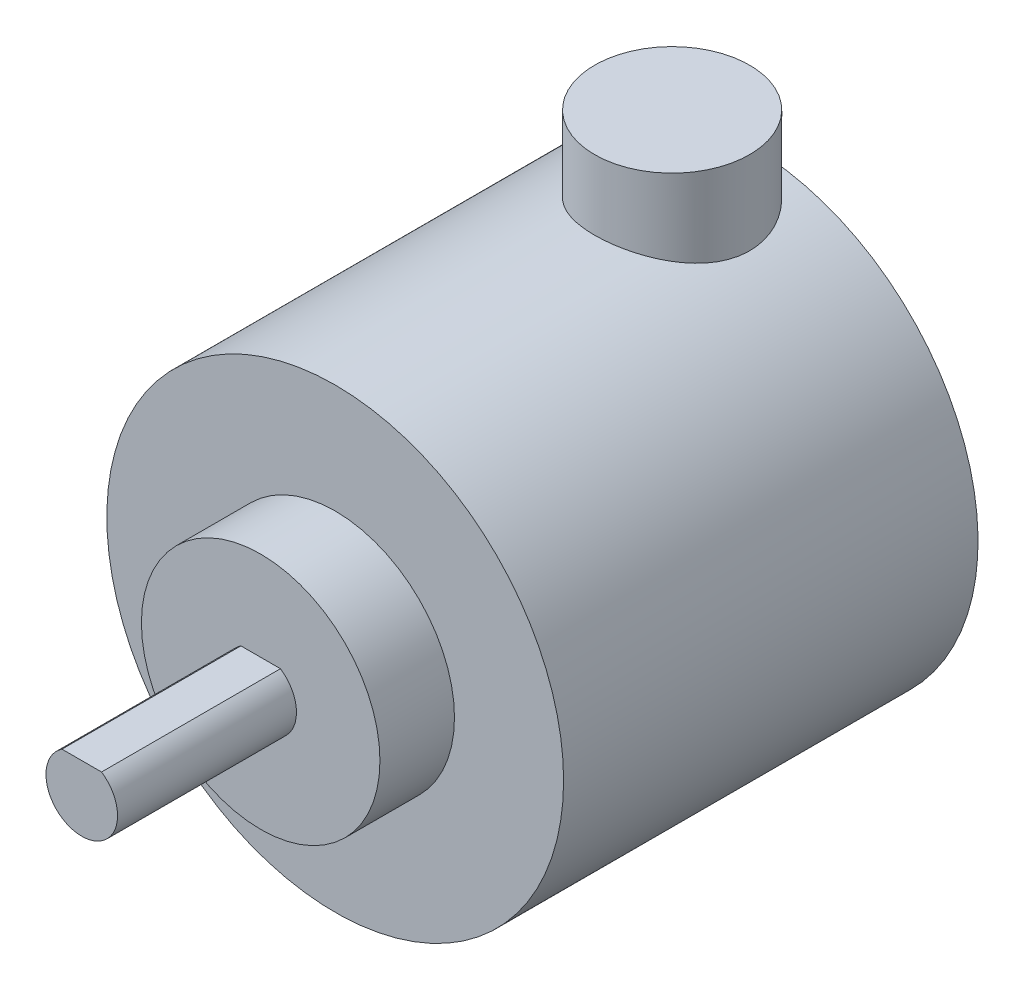
SolidWorks part; units mm, degrees
ref_plane "Front Plane" through (0, 0, 0) normal (0, 0, 1) x (1, 0, 0)
ref_plane "Top Plane" through (0, 0, 0) normal (0, 1, 0) x (1, 0, 0)
ref_plane "Right Plane" through (0, 0, 0) normal (1, 0, 0) x (0, 0, -1)
sketch "Sketch1" plane through (0, 0, 0) normal (0, 0, 1) x (1, 0, 0)
  circle A0 centre (0, 0) radius 19.15
extrude "Boss-Extrude1" add sketch "Sketch1" along normal blind 34.75
sketch "Sketch2" plane through (0, 0, 34.75) normal (0, 0, 1) x (1, 0, 0)
  circle A0 centre (0, 0) radius 10
extrude "Boss-Extrude2" add sketch "Sketch2" along normal blind 6.25
sketch "Sketch3" plane through (0, 0, 41) normal (0, 0, 1) x (1, 0, 0)
  circle A0 centre (0, 0) radius 3
extrude "Boss-Extrude3" add sketch "Sketch3" along normal blind 15
sketch "Sketch4" plane through (0, 0, 56) normal (0, 0, 1) x (1, 0, 0)
  line L0 (-1.6583, 2.5) -> (1.6583, 2.5)
  circle A0 centre (0, 0) radius 3 construction
  arc A1 (-1.6583, 2.5) -> (1.6583, 2.5) centre (0, 0) cw
  dimension "D1" = 2.5
extrude "Cut-Extrude1" cut sketch "Sketch4" against normal blind 15
sketch3d "3DSketch1" plane through (0, 0, 0) normal (0, 0, 1) x (1, 0, 0)
sketch "Sketch5" plane through (0, 0, 0) normal (0, 1, 0) x (1, 0, 0)
  circle A0 centre (0, -6.5) radius 6.5
extrude "Boss-Extrude4" add sketch "Sketch5" along normal blind 25
